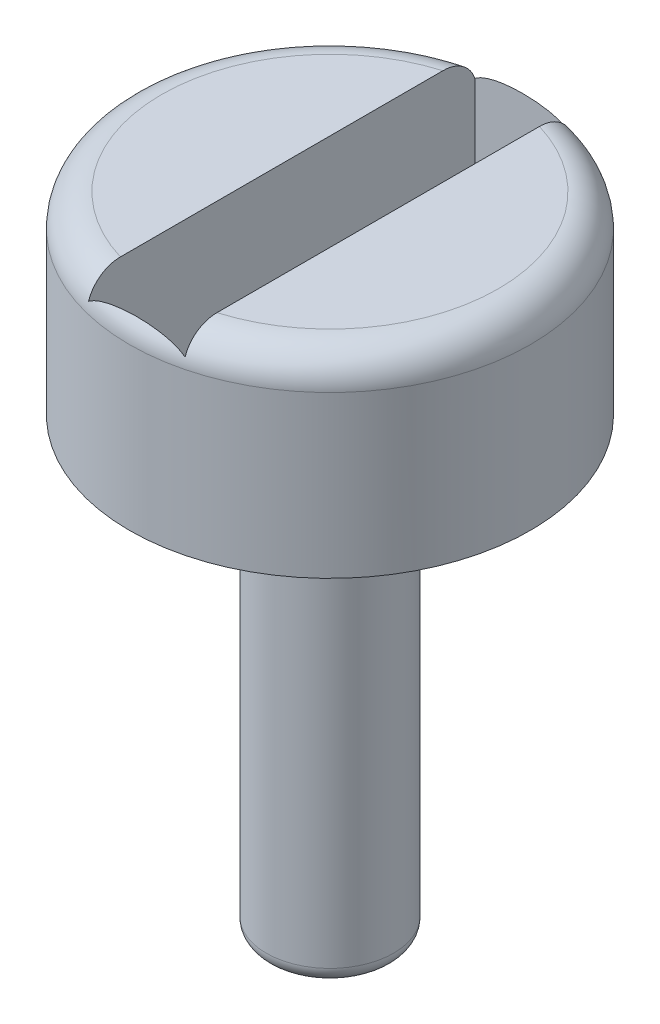
SolidWorks part; units mm, degrees
material "2014-T6"
ref_plane "Front Plane" through (0, 0, 0) normal (0, 0, 1) x (1, 0, 0)
ref_plane "Top Plane" through (0, 0, 0) normal (0, 1, 0) x (1, 0, 0)
ref_plane "Right Plane" through (0, 0, 0) normal (1, 0, 0) x (0, 0, -1)
sketch "Sketch2" plane through (0, 0, 0) normal (0, 0, 1) x (1, 0, 0)
  line L0 (0, 0) -> (3.115, 0)
  line L1 (3.115, 0) -> (3.115, -3)
  line L2 (3.115, -3) -> (0.99, -3)
  line L3 (0.99, -3) -> (0.99, -10)
  line L4 (0.99, -10) -> (0, -10)
  line L5 (0, -10) -> (0, 0)
  line L6 (0, 0) -> (0, -10.6577) construction
  dimension "D1" = 10
  dimension "D3" = 0.99
  dimension "D4" = 3
revolve "Revolve1" add sketch "Sketch2" angle 360 about L6
sketch "Sketch3" plane through (0, -10, 0) normal (0, -1, 0) x (1, 0, 0)
  circle A1 centre (0, 0) radius 0.99
curve "Helix/Spiral1" pitch 0.25 height 6.9375 turns 27.75
fillet "Fillet1" radius 0.5 1 edges at (0, 0, 3.115)
fillet "Fillet2" radius 0.25 1 edges at (0, -10, 0.99)
sketch "Sketch4" plane through (0, 0, 0) normal (0, 1, 0) x (1, 0, 0)
  line L0 (0.75, 0.0515) -> (0.75, 3)
  line L1 (0.75, 3) -> (0.75, -3)
  line L2 (0.75, -3) -> (-0.75, -3)
  line L3 (-0.75, -3) -> (-0.75, 3)
  line L4 (-0.75, 3) -> (0.75, 3)
  dimension "D1" = 1.5
extrude "Cut-Extrude1" cut sketch "Sketch4" along direction (0, -1, 0) on the side against the normal blind 2 contours L4 L3 L2 L1 L0
